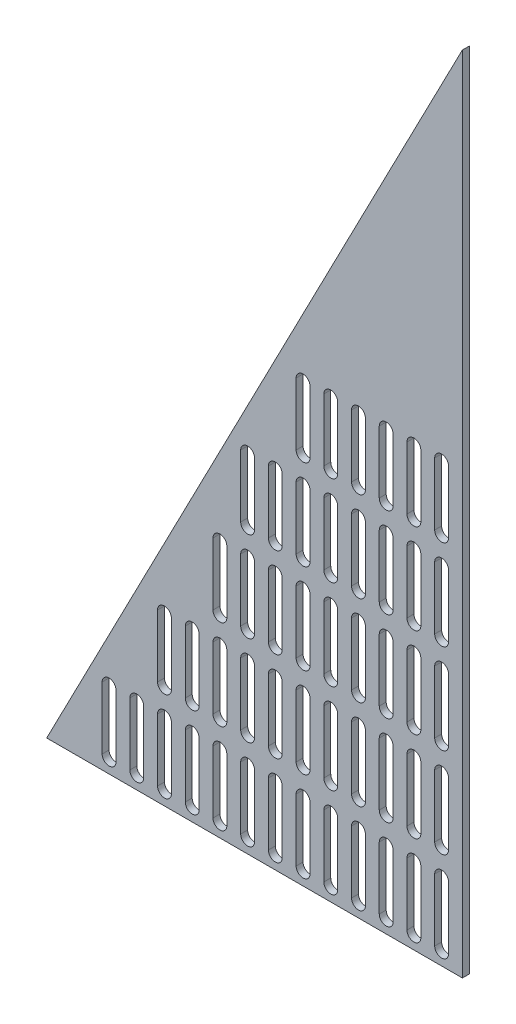
SolidWorks part; units mm, degrees
ref_plane "Front Plane" through (0, 0, 0) normal (0, 0, 1) x (1, 0, 0)
ref_plane "Top Plane" through (0, 0, 0) normal (0, 1, 0) x (1, 0, 0)
ref_plane "Right Plane" through (0, 0, 0) normal (1, 0, 0) x (0, 0, -1)
sketch "Sketch1" plane through (0, 0, 0) normal (0, 0, 1) x (1, 0, 0)
  line L0 (0, 0) -> (0, 736.6)
  line L1 (0, 736.6) -> (-381, 0)
  line L2 (-381, 0) -> (0, 0)
  dimension "D1" = 381
  dimension "D2" = 736.6
extrude "Boss-Extrude1" add sketch "Sketch1" along normal blind 6.35
sketch "Sketch2" plane through (0, 0, 6.35) normal (0, 0, 1) x (1, 0, 0)
  line L0 (-19.05, 12.7) -> (-19.05, 69.85) construction
  line L1 (-25.4, 12.7) -> (-25.4, 69.85)
  line L2 (-12.7, 12.7) -> (-12.7, 69.85)
  line L3 (0, 0) -> (0, 736.6) construction
  line L4 (-381, 0) -> (0, 0) construction
  line L5 (-38.1, 12.7) -> (-38.1, 69.85)
  line L6 (-50.8, 12.7) -> (-50.8, 69.85)
  line L7 (-44.45, 12.7) -> (-44.45, 69.85) construction
  line L8 (-63.5, 12.7) -> (-63.5, 69.85)
  line L9 (-76.2, 12.7) -> (-76.2, 69.85)
  line L10 (-69.85, 12.7) -> (-69.85, 69.85) construction
  line L11 (-88.9, 12.7) -> (-88.9, 69.85)
  line L12 (-101.6, 12.7) -> (-101.6, 69.85)
  line L13 (-95.25, 12.7) -> (-95.25, 69.85) construction
  line L14 (-114.3, 12.7) -> (-114.3, 69.85)
  line L15 (-127, 12.7) -> (-127, 69.85)
  line L16 (-120.65, 12.7) -> (-120.65, 69.85) construction
  line L17 (-139.7, 12.7) -> (-139.7, 69.85)
  line L18 (-152.4, 12.7) -> (-152.4, 69.85)
  line L19 (-146.05, 12.7) -> (-146.05, 69.85) construction
  line L20 (-165.1, 12.7) -> (-165.1, 69.85)
  line L21 (-177.8, 12.7) -> (-177.8, 69.85)
  line L22 (-171.45, 12.7) -> (-171.45, 69.85) construction
  line L23 (-190.5, 12.7) -> (-190.5, 69.85)
  line L24 (-203.2, 12.7) -> (-203.2, 69.85)
  line L25 (-196.85, 12.7) -> (-196.85, 69.85) construction
  line L26 (-215.9, 12.7) -> (-215.9, 69.85)
  line L27 (-228.6, 12.7) -> (-228.6, 69.85)
  line L28 (-222.25, 12.7) -> (-222.25, 69.85) construction
  line L29 (-241.3, 12.7) -> (-241.3, 69.85)
  line L30 (-254, 12.7) -> (-254, 69.85)
  line L31 (-247.65, 12.7) -> (-247.65, 69.85) construction
  line L32 (-266.7, 12.7) -> (-266.7, 69.85)
  line L33 (-279.4, 12.7) -> (-279.4, 69.85)
  line L34 (-273.05, 12.7) -> (-273.05, 69.85) construction
  line L35 (-292.1, 12.7) -> (-292.1, 69.85)
  line L36 (-304.8, 12.7) -> (-304.8, 69.85)
  line L37 (-298.45, 12.7) -> (-298.45, 69.85) construction
  line L38 (-317.5, 12.7) -> (-317.5, 69.85)
  line L39 (-330.2, 12.7) -> (-330.2, 69.85)
  line L40 (-323.85, 12.7) -> (-323.85, 69.85) construction
  line L41 (-38.1, 95.25) -> (-38.1, 152.4)
  line L42 (-50.8, 95.25) -> (-50.8, 152.4)
  line L43 (-44.45, 95.25) -> (-44.45, 152.4) construction
  line L44 (-63.5, 95.25) -> (-63.5, 152.4)
  line L45 (-76.2, 95.25) -> (-76.2, 152.4)
  line L46 (-69.85, 95.25) -> (-69.85, 152.4) construction
  line L47 (-88.9, 95.25) -> (-88.9, 152.4)
  line L48 (-101.6, 95.25) -> (-101.6, 152.4)
  line L49 (-95.25, 95.25) -> (-95.25, 152.4) construction
  line L50 (-114.3, 95.25) -> (-114.3, 152.4)
  line L51 (-127, 95.25) -> (-127, 152.4)
  line L52 (-120.65, 95.25) -> (-120.65, 152.4) construction
  line L53 (-139.7, 95.25) -> (-139.7, 152.4)
  line L54 (-152.4, 95.25) -> (-152.4, 152.4)
  line L55 (-146.05, 95.25) -> (-146.05, 152.4) construction
  line L56 (-165.1, 95.25) -> (-165.1, 152.4)
  line L57 (-177.8, 95.25) -> (-177.8, 152.4)
  line L58 (-171.45, 95.25) -> (-171.45, 152.4) construction
  line L59 (-190.5, 95.25) -> (-190.5, 152.4)
  line L60 (-203.2, 95.25) -> (-203.2, 152.4)
  line L61 (-196.85, 95.25) -> (-196.85, 152.4) construction
  line L62 (-215.9, 95.25) -> (-215.9, 152.4)
  line L63 (-228.6, 95.25) -> (-228.6, 152.4)
  line L64 (-222.25, 95.25) -> (-222.25, 152.4) construction
  line L65 (-241.3, 95.25) -> (-241.3, 152.4)
  line L66 (-254, 95.25) -> (-254, 152.4)
  line L67 (-247.65, 95.25) -> (-247.65, 152.4) construction
  line L68 (-266.7, 95.25) -> (-266.7, 152.4)
  line L69 (-279.4, 95.25) -> (-279.4, 152.4)
  line L70 (-273.05, 95.25) -> (-273.05, 152.4) construction
  line L77 (-38.1, 177.8) -> (-38.1, 234.95)
  line L78 (-50.8, 177.8) -> (-50.8, 234.95)
  line L79 (-44.45, 177.8) -> (-44.45, 234.95) construction
  line L80 (-63.5, 177.8) -> (-63.5, 234.95)
  line L81 (-76.2, 177.8) -> (-76.2, 234.95)
  line L82 (-69.85, 177.8) -> (-69.85, 234.95) construction
  line L83 (-88.9, 177.8) -> (-88.9, 234.95)
  line L84 (-101.6, 177.8) -> (-101.6, 234.95)
  line L85 (-95.25, 177.8) -> (-95.25, 234.95) construction
  line L86 (-114.3, 177.8) -> (-114.3, 234.95)
  line L87 (-127, 177.8) -> (-127, 234.95)
  line L88 (-120.65, 177.8) -> (-120.65, 234.95) construction
  line L89 (-139.7, 177.8) -> (-139.7, 234.95)
  line L90 (-152.4, 177.8) -> (-152.4, 234.95)
  line L91 (-146.05, 177.8) -> (-146.05, 234.95) construction
  line L92 (-165.1, 177.8) -> (-165.1, 234.95)
  line L93 (-177.8, 177.8) -> (-177.8, 234.95)
  line L94 (-171.45, 177.8) -> (-171.45, 234.95) construction
  line L95 (-190.5, 177.8) -> (-190.5, 234.95)
  line L96 (-203.2, 177.8) -> (-203.2, 234.95)
  line L97 (-196.85, 177.8) -> (-196.85, 234.95) construction
  line L98 (-215.9, 177.8) -> (-215.9, 234.95)
  line L99 (-228.6, 177.8) -> (-228.6, 234.95)
  line L100 (-222.25, 177.8) -> (-222.25, 234.95) construction
  line L113 (-38.1, 260.35) -> (-38.1, 317.5)
  line L114 (-50.8, 260.35) -> (-50.8, 317.5)
  line L115 (-44.45, 260.35) -> (-44.45, 317.5) construction
  line L116 (-63.5, 260.35) -> (-63.5, 317.5)
  line L117 (-76.2, 260.35) -> (-76.2, 317.5)
  line L118 (-69.85, 260.35) -> (-69.85, 317.5) construction
  line L119 (-88.9, 260.35) -> (-88.9, 317.5)
  line L120 (-101.6, 260.35) -> (-101.6, 317.5)
  line L121 (-95.25, 260.35) -> (-95.25, 317.5) construction
  line L122 (-114.3, 260.35) -> (-114.3, 317.5)
  line L123 (-127, 260.35) -> (-127, 317.5)
  line L124 (-120.65, 260.35) -> (-120.65, 317.5) construction
  line L125 (-139.7, 260.35) -> (-139.7, 317.5)
  line L126 (-152.4, 260.35) -> (-152.4, 317.5)
  line L127 (-146.05, 260.35) -> (-146.05, 317.5) construction
  line L128 (-165.1, 260.35) -> (-165.1, 317.5)
  line L129 (-177.8, 260.35) -> (-177.8, 317.5)
  line L130 (-171.45, 260.35) -> (-171.45, 317.5) construction
  line L131 (-190.5, 260.35) -> (-190.5, 317.5)
  line L132 (-203.2, 260.35) -> (-203.2, 317.5)
  line L133 (-196.85, 260.35) -> (-196.85, 317.5) construction
  line L149 (-38.1, 342.9) -> (-38.1, 400.05)
  line L150 (-50.8, 342.9) -> (-50.8, 400.05)
  line L151 (-44.45, 342.9) -> (-44.45, 400.05) construction
  line L152 (-63.5, 342.9) -> (-63.5, 400.05)
  line L153 (-76.2, 342.9) -> (-76.2, 400.05)
  line L154 (-69.85, 342.9) -> (-69.85, 400.05) construction
  line L155 (-88.9, 342.9) -> (-88.9, 400.05)
  line L156 (-101.6, 342.9) -> (-101.6, 400.05)
  line L157 (-95.25, 342.9) -> (-95.25, 400.05) construction
  line L158 (-114.3, 342.9) -> (-114.3, 400.05)
  line L159 (-127, 342.9) -> (-127, 400.05)
  line L160 (-120.65, 342.9) -> (-120.65, 400.05) construction
  line L161 (-139.7, 342.9) -> (-139.7, 400.05)
  line L162 (-152.4, 342.9) -> (-152.4, 400.05)
  line L163 (-146.05, 342.9) -> (-146.05, 400.05) construction
  line L185 (-12.7, 95.25) -> (-12.7, 152.4)
  line L186 (-25.4, 95.25) -> (-25.4, 152.4)
  line L187 (-19.05, 95.25) -> (-19.05, 152.4) construction
  line L188 (-12.7, 177.8) -> (-12.7, 234.95)
  line L189 (-25.4, 177.8) -> (-25.4, 234.95)
  line L190 (-19.05, 177.8) -> (-19.05, 234.95) construction
  line L191 (-12.7, 260.35) -> (-12.7, 317.5)
  line L192 (-25.4, 260.35) -> (-25.4, 317.5)
  line L193 (-19.05, 260.35) -> (-19.05, 317.5) construction
  line L194 (-12.7, 342.9) -> (-12.7, 400.05)
  line L195 (-25.4, 342.9) -> (-25.4, 400.05)
  line L196 (-19.05, 342.9) -> (-19.05, 400.05) construction
  arc A0 (-25.4, 12.7) -> (-12.7, 12.7) centre (-19.05, 12.7) ccw
  arc A1 (-12.7, 69.85) -> (-25.4, 69.85) centre (-19.05, 69.85) ccw
  arc A2 (-50.8, 12.7) -> (-38.1, 12.7) centre (-44.45, 12.7) ccw
  arc A3 (-38.1, 69.85) -> (-50.8, 69.85) centre (-44.45, 69.85) ccw
  arc A4 (-76.2, 12.7) -> (-63.5, 12.7) centre (-69.85, 12.7) ccw
  arc A5 (-63.5, 69.85) -> (-76.2, 69.85) centre (-69.85, 69.85) ccw
  arc A6 (-101.6, 12.7) -> (-88.9, 12.7) centre (-95.25, 12.7) ccw
  arc A7 (-88.9, 69.85) -> (-101.6, 69.85) centre (-95.25, 69.85) ccw
  arc A8 (-127, 12.7) -> (-114.3, 12.7) centre (-120.65, 12.7) ccw
  arc A9 (-114.3, 69.85) -> (-127, 69.85) centre (-120.65, 69.85) ccw
  arc A10 (-152.4, 12.7) -> (-139.7, 12.7) centre (-146.05, 12.7) ccw
  arc A11 (-139.7, 69.85) -> (-152.4, 69.85) centre (-146.05, 69.85) ccw
  arc A12 (-177.8, 12.7) -> (-165.1, 12.7) centre (-171.45, 12.7) ccw
  arc A13 (-165.1, 69.85) -> (-177.8, 69.85) centre (-171.45, 69.85) ccw
  arc A14 (-203.2, 12.7) -> (-190.5, 12.7) centre (-196.85, 12.7) ccw
  arc A15 (-190.5, 69.85) -> (-203.2, 69.85) centre (-196.85, 69.85) ccw
  arc A16 (-228.6, 12.7) -> (-215.9, 12.7) centre (-222.25, 12.7) ccw
  arc A17 (-215.9, 69.85) -> (-228.6, 69.85) centre (-222.25, 69.85) ccw
  arc A18 (-254, 12.7) -> (-241.3, 12.7) centre (-247.65, 12.7) ccw
  arc A19 (-241.3, 69.85) -> (-254, 69.85) centre (-247.65, 69.85) ccw
  arc A20 (-279.4, 12.7) -> (-266.7, 12.7) centre (-273.05, 12.7) ccw
  arc A21 (-266.7, 69.85) -> (-279.4, 69.85) centre (-273.05, 69.85) ccw
  arc A22 (-304.8, 12.7) -> (-292.1, 12.7) centre (-298.45, 12.7) ccw
  arc A23 (-292.1, 69.85) -> (-304.8, 69.85) centre (-298.45, 69.85) ccw
  arc A24 (-330.2, 12.7) -> (-317.5, 12.7) centre (-323.85, 12.7) ccw
  arc A25 (-317.5, 69.85) -> (-330.2, 69.85) centre (-323.85, 69.85) ccw
  arc A26 (-50.8, 95.25) -> (-38.1, 95.25) centre (-44.45, 95.25) ccw
  arc A27 (-38.1, 152.4) -> (-50.8, 152.4) centre (-44.45, 152.4) ccw
  arc A28 (-76.2, 95.25) -> (-63.5, 95.25) centre (-69.85, 95.25) ccw
  arc A29 (-63.5, 152.4) -> (-76.2, 152.4) centre (-69.85, 152.4) ccw
  arc A30 (-101.6, 95.25) -> (-88.9, 95.25) centre (-95.25, 95.25) ccw
  arc A31 (-88.9, 152.4) -> (-101.6, 152.4) centre (-95.25, 152.4) ccw
  arc A32 (-127, 95.25) -> (-114.3, 95.25) centre (-120.65, 95.25) ccw
  arc A33 (-114.3, 152.4) -> (-127, 152.4) centre (-120.65, 152.4) ccw
  arc A34 (-152.4, 95.25) -> (-139.7, 95.25) centre (-146.05, 95.25) ccw
  arc A35 (-139.7, 152.4) -> (-152.4, 152.4) centre (-146.05, 152.4) ccw
  arc A36 (-177.8, 95.25) -> (-165.1, 95.25) centre (-171.45, 95.25) ccw
  arc A37 (-165.1, 152.4) -> (-177.8, 152.4) centre (-171.45, 152.4) ccw
  arc A38 (-203.2, 95.25) -> (-190.5, 95.25) centre (-196.85, 95.25) ccw
  arc A39 (-190.5, 152.4) -> (-203.2, 152.4) centre (-196.85, 152.4) ccw
  arc A40 (-228.6, 95.25) -> (-215.9, 95.25) centre (-222.25, 95.25) ccw
  arc A41 (-215.9, 152.4) -> (-228.6, 152.4) centre (-222.25, 152.4) ccw
  arc A42 (-254, 95.25) -> (-241.3, 95.25) centre (-247.65, 95.25) ccw
  arc A43 (-241.3, 152.4) -> (-254, 152.4) centre (-247.65, 152.4) ccw
  arc A44 (-279.4, 95.25) -> (-266.7, 95.25) centre (-273.05, 95.25) ccw
  arc A45 (-266.7, 152.4) -> (-279.4, 152.4) centre (-273.05, 152.4) ccw
  arc A50 (-50.8, 177.8) -> (-38.1, 177.8) centre (-44.45, 177.8) ccw
  arc A51 (-38.1, 234.95) -> (-50.8, 234.95) centre (-44.45, 234.95) ccw
  arc A52 (-76.2, 177.8) -> (-63.5, 177.8) centre (-69.85, 177.8) ccw
  arc A53 (-63.5, 234.95) -> (-76.2, 234.95) centre (-69.85, 234.95) ccw
  arc A54 (-101.6, 177.8) -> (-88.9, 177.8) centre (-95.25, 177.8) ccw
  arc A55 (-88.9, 234.95) -> (-101.6, 234.95) centre (-95.25, 234.95) ccw
  arc A56 (-127, 177.8) -> (-114.3, 177.8) centre (-120.65, 177.8) ccw
  arc A57 (-114.3, 234.95) -> (-127, 234.95) centre (-120.65, 234.95) ccw
  arc A58 (-152.4, 177.8) -> (-139.7, 177.8) centre (-146.05, 177.8) ccw
  arc A59 (-139.7, 234.95) -> (-152.4, 234.95) centre (-146.05, 234.95) ccw
  arc A60 (-177.8, 177.8) -> (-165.1, 177.8) centre (-171.45, 177.8) ccw
  arc A61 (-165.1, 234.95) -> (-177.8, 234.95) centre (-171.45, 234.95) ccw
  arc A62 (-203.2, 177.8) -> (-190.5, 177.8) centre (-196.85, 177.8) ccw
  arc A63 (-190.5, 234.95) -> (-203.2, 234.95) centre (-196.85, 234.95) ccw
  arc A64 (-228.6, 177.8) -> (-215.9, 177.8) centre (-222.25, 177.8) ccw
  arc A65 (-215.9, 234.95) -> (-228.6, 234.95) centre (-222.25, 234.95) ccw
  arc A74 (-50.8, 260.35) -> (-38.1, 260.35) centre (-44.45, 260.35) ccw
  arc A75 (-38.1, 317.5) -> (-50.8, 317.5) centre (-44.45, 317.5) ccw
  arc A76 (-76.2, 260.35) -> (-63.5, 260.35) centre (-69.85, 260.35) ccw
  arc A77 (-63.5, 317.5) -> (-76.2, 317.5) centre (-69.85, 317.5) ccw
  arc A78 (-101.6, 260.35) -> (-88.9, 260.35) centre (-95.25, 260.35) ccw
  arc A79 (-88.9, 317.5) -> (-101.6, 317.5) centre (-95.25, 317.5) ccw
  arc A80 (-127, 260.35) -> (-114.3, 260.35) centre (-120.65, 260.35) ccw
  arc A81 (-114.3, 317.5) -> (-127, 317.5) centre (-120.65, 317.5) ccw
  arc A82 (-152.4, 260.35) -> (-139.7, 260.35) centre (-146.05, 260.35) ccw
  arc A83 (-139.7, 317.5) -> (-152.4, 317.5) centre (-146.05, 317.5) ccw
  arc A84 (-177.8, 260.35) -> (-165.1, 260.35) centre (-171.45, 260.35) ccw
  arc A85 (-165.1, 317.5) -> (-177.8, 317.5) centre (-171.45, 317.5) ccw
  arc A86 (-203.2, 260.35) -> (-190.5, 260.35) centre (-196.85, 260.35) ccw
  arc A87 (-190.5, 317.5) -> (-203.2, 317.5) centre (-196.85, 317.5) ccw
  arc A98 (-50.8, 342.9) -> (-38.1, 342.9) centre (-44.45, 342.9) ccw
  arc A99 (-38.1, 400.05) -> (-50.8, 400.05) centre (-44.45, 400.05) ccw
  arc A100 (-76.2, 342.9) -> (-63.5, 342.9) centre (-69.85, 342.9) ccw
  arc A101 (-63.5, 400.05) -> (-76.2, 400.05) centre (-69.85, 400.05) ccw
  arc A102 (-101.6, 342.9) -> (-88.9, 342.9) centre (-95.25, 342.9) ccw
  arc A103 (-88.9, 400.05) -> (-101.6, 400.05) centre (-95.25, 400.05) ccw
  arc A104 (-127, 342.9) -> (-114.3, 342.9) centre (-120.65, 342.9) ccw
  arc A105 (-114.3, 400.05) -> (-127, 400.05) centre (-120.65, 400.05) ccw
  arc A106 (-152.4, 342.9) -> (-139.7, 342.9) centre (-146.05, 342.9) ccw
  arc A107 (-139.7, 400.05) -> (-152.4, 400.05) centre (-146.05, 400.05) ccw
  arc A122 (-25.4, 95.25) -> (-12.7, 95.25) centre (-19.05, 95.25) ccw
  arc A123 (-12.7, 152.4) -> (-25.4, 152.4) centre (-19.05, 152.4) ccw
  arc A124 (-25.4, 177.8) -> (-12.7, 177.8) centre (-19.05, 177.8) ccw
  arc A125 (-12.7, 234.95) -> (-25.4, 234.95) centre (-19.05, 234.95) ccw
  arc A126 (-25.4, 260.35) -> (-12.7, 260.35) centre (-19.05, 260.35) ccw
  arc A127 (-12.7, 317.5) -> (-25.4, 317.5) centre (-19.05, 317.5) ccw
  arc A128 (-25.4, 342.9) -> (-12.7, 342.9) centre (-19.05, 342.9) ccw
  arc A129 (-12.7, 400.05) -> (-25.4, 400.05) centre (-19.05, 400.05) ccw
  point P2 (-19.05, 41.275)
  point P11 (-19.05, 76.2)
  point P16 (-44.45, 41.275)
  point P23 (-69.85, 41.275)
  point P30 (-95.25, 41.275)
  point P37 (-120.65, 41.275)
  point P44 (-146.05, 41.275)
  point P51 (-171.45, 41.275)
  point P58 (-196.85, 41.275)
  point P65 (-222.25, 41.275)
  point P72 (-247.65, 41.275)
  point P79 (-273.05, 41.275)
  point P86 (-298.45, 41.275)
  point P93 (-323.85, 41.275)
  point P100 (-44.45, 123.825)
  point P107 (-69.85, 123.825)
  point P114 (-95.25, 123.825)
  point P121 (-120.65, 123.825)
  point P128 (-146.05, 123.825)
  point P135 (-171.45, 123.825)
  point P142 (-196.85, 123.825)
  point P149 (-222.25, 123.825)
  point P156 (-247.65, 123.825)
  point P163 (-273.05, 123.825)
  point P184 (-44.45, 206.375)
  point P191 (-69.85, 206.375)
  point P198 (-95.25, 206.375)
  point P205 (-120.65, 206.375)
  point P212 (-146.05, 206.375)
  point P219 (-171.45, 206.375)
  point P226 (-196.85, 206.375)
  point P233 (-222.25, 206.375)
  point P268 (-44.45, 288.925)
  point P275 (-69.85, 288.925)
  point P282 (-95.25, 288.925)
  point P289 (-120.65, 288.925)
  point P296 (-146.05, 288.925)
  point P303 (-171.45, 288.925)
  point P310 (-196.85, 288.925)
  point P352 (-44.45, 371.475)
  point P359 (-69.85, 371.475)
  point P366 (-95.25, 371.475)
  point P373 (-120.65, 371.475)
  point P380 (-146.05, 371.475)
  point P436 (-19.05, 123.825)
  point P443 (-19.05, 206.375)
  point P450 (-19.05, 288.925)
  point P457 (-19.05, 371.475)
  dimension "D1" = 12.7
  dimension "D2" = 12.7
  dimension "D3" = 12.7
  dimension "D4" = 63.5
extrude "Cut-Extrude1" cut sketch "Sketch2" against normal through all
